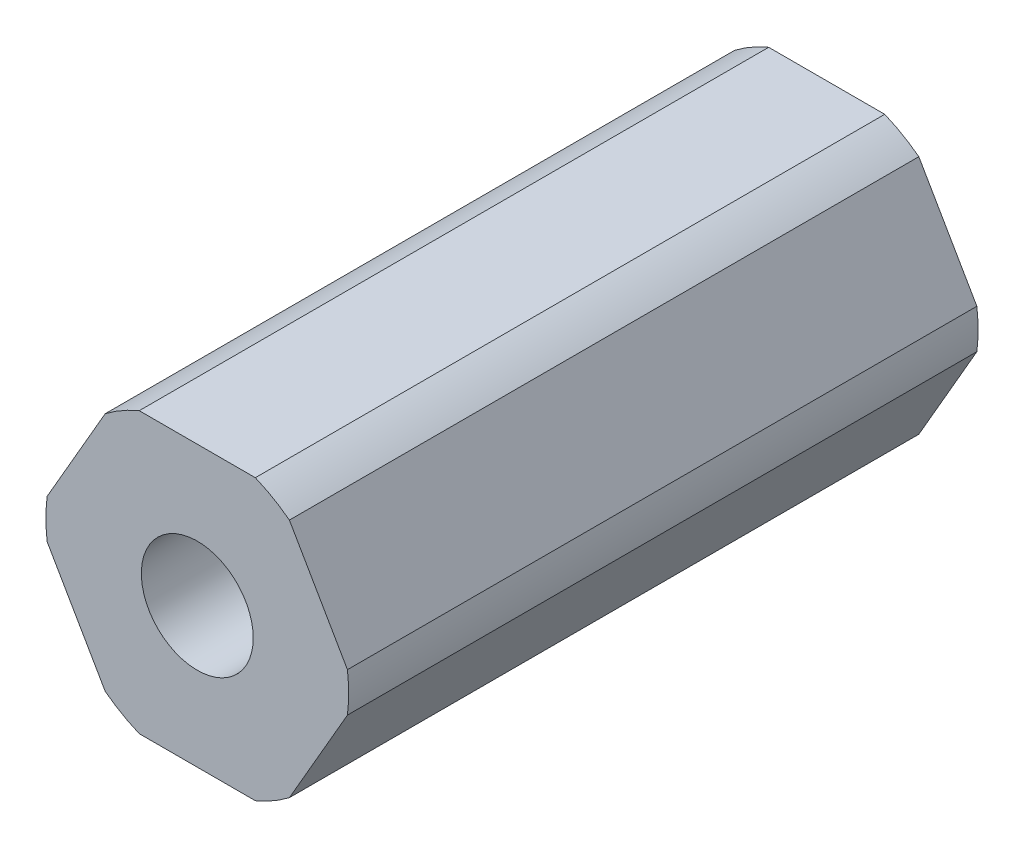
SolidWorks part; units mm, degrees
material "7075-T6 (SN)"
ref_plane "Front Plane" through (0, 0, 0) normal (0, 0, 1) x (1, 0, 0)
ref_plane "Top Plane" through (0, 0, 0) normal (0, 1, 0) x (1, 0, 0)
ref_plane "Right Plane" through (0, 0, 0) normal (1, 0, 0) x (0, 0, -1)
sketch "Sketch1" plane through (0, 0, 0) normal (0, 0, 1) x (1, 0, 0)
  line L1 (4.1818, -5.457) -> (6.8168, -0.893)
  line L2 (6.8168, 0.893) -> (4.1818, 5.457)
  line L3 (2.635, 6.35) -> (-2.635, 6.35)
  line L4 (-4.1818, 5.457) -> (-6.8168, 0.893)
  line L5 (-6.8168, -0.893) -> (-4.1818, -5.457)
  line L6 (-2.635, -6.35) -> (2.635, -6.35)
  circle A0 centre (0, 0) radius 6.35 construction
  arc A1 (-6.8168, 0.893) -> (-6.8168, -0.893) centre (0, 0) ccw
  arc A2 (-2.635, 6.35) -> (-4.1818, 5.457) centre (0, 0) ccw
  arc A3 (4.1818, 5.457) -> (2.635, 6.35) centre (0, 0) ccw
  arc A4 (6.8168, -0.893) -> (6.8168, 0.893) centre (0, 0) ccw
  arc A5 (2.635, -6.35) -> (4.1818, -5.457) centre (0, 0) ccw
  arc A6 (-4.1818, -5.457) -> (-2.635, -6.35) centre (0, 0) ccw
  circle A7 centre (0, 0) radius 2.54
  dimension "D1" = 12.7
  dimension "D2" = 13.75
  dimension "D3" = 5.08
extrude "Boss-Extrude1" add sketch "Sketch1" along normal blind 28.575
